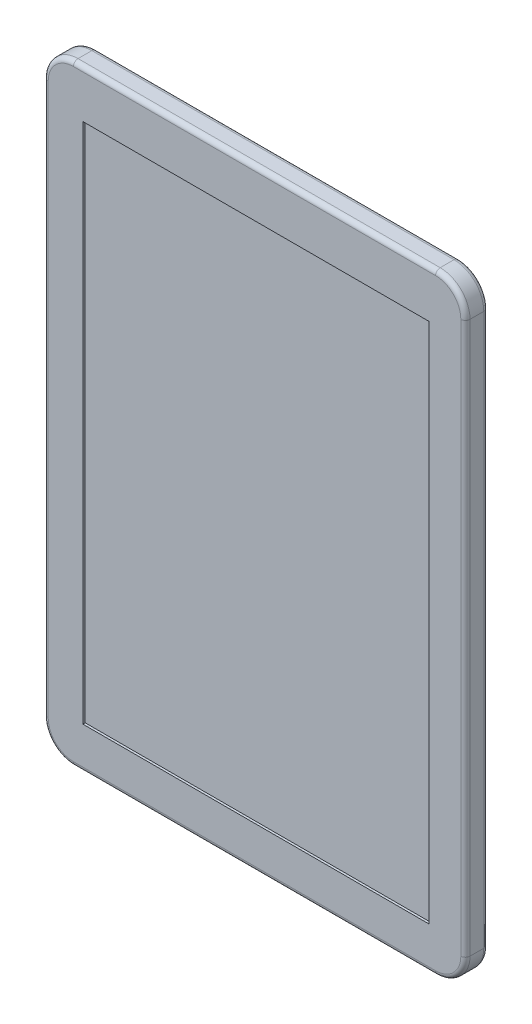
SolidWorks part; units mm, degrees
ref_plane "Front Plane" through (0, 0, 0) normal (0, 0, 1) x (1, 0, 0)
ref_plane "Top Plane" through (0, 0, 0) normal (0, 1, 0) x (1, 0, 0)
ref_plane "Right Plane" through (0, 0, 0) normal (1, 0, 0) x (0, 0, -1)
sketch "Sketch1" plane through (0, 0, 0) normal (0, 0, 1) x (1, 0, 0)
  line L1 (-10.7234, 42.7039) -> (146.8666, 42.7039)
  line L2 (-23.7034, 29.7239) -> (-23.7034, -210.2661)
  line L3 (-10.7234, -223.2461) -> (146.8666, -223.2461)
  line L4 (159.8466, 29.7239) -> (159.8466, -210.2661)
  arc A0 (-23.7034, -210.2661) -> (-10.7234, -223.2461) centre (-10.7234, -210.2661) ccw
  arc A1 (146.8666, -223.2461) -> (159.8466, -210.2661) centre (146.8666, -210.2661) ccw
  arc A2 (159.8466, 29.7239) -> (146.8666, 42.7039) centre (146.8666, 29.7239) ccw
  arc A3 (-23.7034, 29.7239) -> (-10.7234, 42.7039) centre (-10.7234, 29.7239) cw
  point P8 (159.8466, -223.2461)
  point P11 (159.8466, 42.7039)
  point P14 (-23.7034, 42.7039)
  dimension "D3" = 12.98
  dimension "D1" = 183.55
  dimension "D2" = 265.95
extrude "Boss-Extrude1" add sketch "Sketch1" along normal blind 10
fillet "Fillet1" radius 2 8 edges at (156.0448, 38.9021, 10) (156.0448, -219.4443, 10) (68.0716, -223.2461, 10) (-19.9017, -219.4443, 10) (159.8466, -90.2711, 10) (68.0716, 42.7039, 10) (-19.9017, 38.9021, 10) (-23.7034, -90.2711, 10)
fillet "Fillet2" radius 2 8 edges at (156.0448, -219.4443, 0) (68.0716, -223.2461, 0) (-19.9017, -219.4443, 0) (-23.7034, -90.2711, 0) (-19.9017, 38.9021, 0) (68.0716, 42.7039, 0) (156.0448, 38.9021, 0) (159.8466, -90.2711, 0)
sketch "Sketch2" plane through (0, 0, 10) normal (0, 0, 1) x (1, 0, 0)
  line L1 (-6.6221, 22.0336) -> (143.9374, 22.0336)
  line L2 (-6.6221, 22.0336) -> (-6.6221, -205.0547)
  line L3 (-6.6221, -205.0547) -> (143.9374, -205.0547)
  line L4 (143.9374, 22.0336) -> (143.9374, -205.0547)
extrude "Cut-Extrude1" cut sketch "Sketch2" against normal blind 1
sketch "Sketch3" plane through (0, 0, 0) normal (0, 0, -1) x (-1, 0, 0)
  line L0 (-159.8466, -210.2661) -> (-159.8466, 29.7239) construction
  line L1 (-102.5866, -13.2761) -> (-33.5466, -13.2761)
  line L2 (-115.5666, -26.2561) -> (-115.5666, -158.2961)
  line L3 (-102.5866, -171.2761) -> (-33.5466, -171.2761)
  line L4 (-20.5666, -26.2561) -> (-20.5666, -158.2961)
  line L5 (10.7234, 40.7039) -> (-146.8666, 40.7039) construction
  arc A0 (-115.5666, -158.2961) -> (-102.5866, -171.2761) centre (-102.5866, -158.2961) ccw
  arc A1 (-33.5466, -171.2761) -> (-20.5666, -158.2961) centre (-33.5466, -158.2961) ccw
  arc A2 (-20.5666, -26.2561) -> (-33.5466, -13.2761) centre (-33.5466, -26.2561) ccw
  arc A3 (-115.5666, -26.2561) -> (-102.5866, -13.2761) centre (-102.5866, -26.2561) cw
  point P12 (-20.5666, -171.2761)
  point P15 (-20.5666, -13.2761)
  point P18 (-115.5666, -13.2761)
  dimension "D5" = 12.98
  dimension "D1" = 95
  dimension "D2" = 158
  dimension "D3" = 44.28
  dimension "D4" = 53.98
extrude "Boss-Extrude2" add sketch "Sketch3" along normal blind 20
sketch "Sketch4" plane through (115.5666, 0, 0) normal (1, 0, 0) x (0, 0, -1)
  line L0 (20, -26.2561) -> (0, -26.2561) construction
  line L1 (7.0202, -71.2561) -> (13.7459, -71.2561)
  line L2 (7.0202, -71.2561) -> (7.0202, -86.2561)
  line L3 (7.0202, -86.2561) -> (13.7459, -86.2561)
  line L4 (13.7459, -71.2561) -> (13.7459, -86.2561)
  line L5 (13.7459, -91.2561) -> (7.0202, -91.2561)
  line L6 (13.7459, -91.2561) -> (13.7459, -106.2561)
  line L7 (13.7459, -106.2561) -> (7.0202, -106.2561)
  line L8 (7.0202, -91.2561) -> (7.0202, -106.2561)
  line L9 (13.7459, -111.2561) -> (7.0202, -111.2561)
  line L10 (13.7459, -111.2561) -> (13.7459, -126.2561)
  line L11 (13.7459, -126.2561) -> (7.0202, -126.2561)
  line L12 (7.0202, -111.2561) -> (7.0202, -126.2561)
  line L13 (13.7459, -131.2561) -> (7.0202, -131.2561)
  line L14 (13.7459, -131.2561) -> (13.7459, -146.2561)
  line L15 (13.7459, -146.2561) -> (7.0202, -146.2561)
  line L16 (7.0202, -131.2561) -> (7.0202, -146.2561)
  dimension "D1" = 15
  dimension "D2" = 15
  dimension "D3" = 15
  dimension "D4" = 15
  dimension "D5" = 5
  dimension "D6" = 5
  dimension "D7" = 5
  dimension "D8" = 45
extrude "Cut-Extrude2" cut sketch "Sketch4" against normal blind 5
sketch "Sketch5" plane through (115.5666, 0, 0) normal (1, 0, 0) x (0, 0, -1)
  line L0 (4.5313, -41.221) -> (12.4153, -41.221)
  line L1 (3.0237, -33.6532) -> (13.8471, -33.6532)
  line L2 (3.0237, -33.6532) -> (3.0237, -63.9813)
  line L3 (3.0237, -63.9813) -> (13.8471, -63.9813)
  line L4 (13.8471, -33.6532) -> (13.8471, -63.9813)
  line L5 (4.5313, -35.8966) -> (12.4153, -35.8966)
  line L6 (4.5313, -35.8966) -> (4.5313, -38.221)
  line L7 (4.5313, -38.221) -> (12.4153, -38.221)
  line L8 (12.4153, -35.8966) -> (12.4153, -38.221)
  line L9 (12.4153, -38.8966) -> (12.4153, -41.221)
  line L10 (4.5313, -38.8966) -> (12.4153, -38.8966)
  line L11 (4.5313, -38.8966) -> (4.5313, -41.221)
  line L12 (4.5313, -44.221) -> (12.4153, -44.221)
  line L13 (12.4153, -41.8966) -> (12.4153, -44.221)
  line L14 (4.5313, -41.8966) -> (12.4153, -41.8966)
  line L15 (4.5313, -41.8966) -> (4.5313, -44.221)
  line L16 (4.5313, -47.221) -> (12.4153, -47.221)
  line L17 (12.4153, -44.8966) -> (12.4153, -47.221)
  line L18 (4.5313, -44.8966) -> (12.4153, -44.8966)
  line L19 (4.5313, -44.8966) -> (4.5313, -47.221)
  line L20 (4.5313, -50.221) -> (12.4153, -50.221)
  line L21 (12.4153, -47.8966) -> (12.4153, -50.221)
  line L22 (4.5313, -47.8966) -> (12.4153, -47.8966)
  line L23 (4.5313, -47.8966) -> (4.5313, -50.221)
  line L24 (4.5313, -53.221) -> (12.4153, -53.221)
  line L25 (12.4153, -50.8966) -> (12.4153, -53.221)
  line L26 (4.5313, -50.8966) -> (12.4153, -50.8966)
  line L27 (4.5313, -50.8966) -> (4.5313, -53.221)
  line L28 (4.5313, -56.221) -> (12.4153, -56.221)
  line L29 (12.4153, -53.8966) -> (12.4153, -56.221)
  line L30 (4.5313, -53.8966) -> (12.4153, -53.8966)
  line L31 (4.5313, -53.8966) -> (4.5313, -56.221)
  line L32 (4.5313, -59.221) -> (12.4153, -59.221)
  line L33 (12.4153, -56.8966) -> (12.4153, -59.221)
  line L34 (4.5313, -56.8966) -> (12.4153, -56.8966)
  line L35 (4.5313, -56.8966) -> (4.5313, -59.221)
  line L36 (4.5313, -62.221) -> (12.4153, -62.221)
  line L37 (12.4153, -59.8966) -> (12.4153, -62.221)
  line L38 (4.5313, -59.8966) -> (12.4153, -59.8966)
  line L39 (4.5313, -59.8966) -> (4.5313, -62.221)
  dimension "D1" = 9
extrude "Cut-Extrude3" cut sketch "Sketch5" against normal blind 5
sketch "Sketch6" plane through (115.5666, 0, 0) normal (1, 0, 0) x (0, 0, -1)
  circle A0 centre (9.5154, -152.9078) radius 4.682
extrude "Boss-Extrude3" add sketch "Sketch6" along normal blind 2
sketch "Sketch7" plane through (117.5666, 0, 0) normal (1, 0, 0) x (0, 0, -1)
  line L0 (9.0373, -152.5438) -> (12.4042, -151.2283)
  line L1 (9.0373, -152.5438) -> (13.7054, -152.5438)
  line L2 (9.0373, -152.5438) -> (9.0373, -153.3515)
  line L3 (9.0373, -153.3515) -> (13.7054, -153.3515)
  line L4 (13.7054, -152.5438) -> (13.7054, -153.3515)
  line L5 (9.0373, -153.3515) -> (12.4042, -154.5185)
  circle A0 centre (9.4155, -152.8734) radius 3.4115
  circle A1 centre (9.4155, -152.8734) radius 2.789
extrude "Cut-Extrude4" cut sketch "Sketch7" against normal blind 1 contours A1 L0 A0 L5 | L3 A1 L1 L2 | A1 L3 A0 L1 | A0 L3 L4 L1
sketch "Sketch8" plane through (0, -171.2761, 0) normal (0, -1, 0) x (1, 0, 0)
  circle A0 centre (39.9483, -5.6708) radius 3.2032
extrude "Boss-Extrude4" add sketch "Sketch8" along normal blind 5
sketch "Sketch9" plane through (0, -176.2761, 0) normal (0, -1, 0) x (1, 0, 0)
  circle A0 centre (39.9483, -5.6708) radius 2.5545
  circle A1 centre (39.9483, -5.6708) radius 0.71
extrude "Cut-Extrude5" cut sketch "Sketch9" against normal blind 5
sketch "Sketch10" plane through (0, -171.2761, 0) normal (0, -1, 0) x (1, 0, 0)
  circle A0 centre (49.9407, -5.3099) radius 3.6994
extrude "Cut-Extrude6" cut sketch "Sketch10" against normal blind 5
sketch "Sketch11" plane through (20.5666, 0, 0) normal (-1, 0, 0) x (0, 0, 1)
  line L1 (-6.8241, -143.7594) -> (-11.294, -146.3401)
  line L2 (-11.294, -146.3401) -> (-11.294, -151.5015)
  line L3 (-11.294, -151.5015) -> (-6.8241, -154.0822)
  line L4 (-6.8241, -154.0822) -> (-2.3542, -151.5015)
  line L5 (-2.3542, -151.5015) -> (-2.3542, -146.3401)
  line L6 (-2.3542, -146.3401) -> (-6.8241, -143.7594)
  circle A0 centre (-6.8241, -148.9208) radius 4.4699 construction
extrude "Boss-Extrude5" add sketch "Sketch11" along normal blind 2
sketch "Sketch12" plane through (18.5666, 0, 0) normal (-1, 0, 0) x (0, 0, 1)
  circle A0 centre (-6.5775, -148.9064) radius 3.6308
extrude "Boss-Extrude6" add sketch "Sketch12" along normal blind 4
sketch "Sketch13" plane through (0, 0, 0) normal (0, 0, -1) x (-1, 0, 0)
  line L0 (-159.8466, -210.2661) -> (-159.8466, 29.7239) construction
  line L1 (10.7234, -223.2461) -> (-146.8666, -223.2461) construction
  circle A0 centre (-105.8466, -185.2461) radius 1
  circle A1 centre (-30.8466, -185.2461) radius 1
  dimension "D2" = 2
  dimension "D3" = 2
  dimension "D1" = 75
  dimension "D4" = 54
  dimension "D5" = 38
extrude "Cut-Extrude7" cut sketch "Sketch13" against normal blind 2
